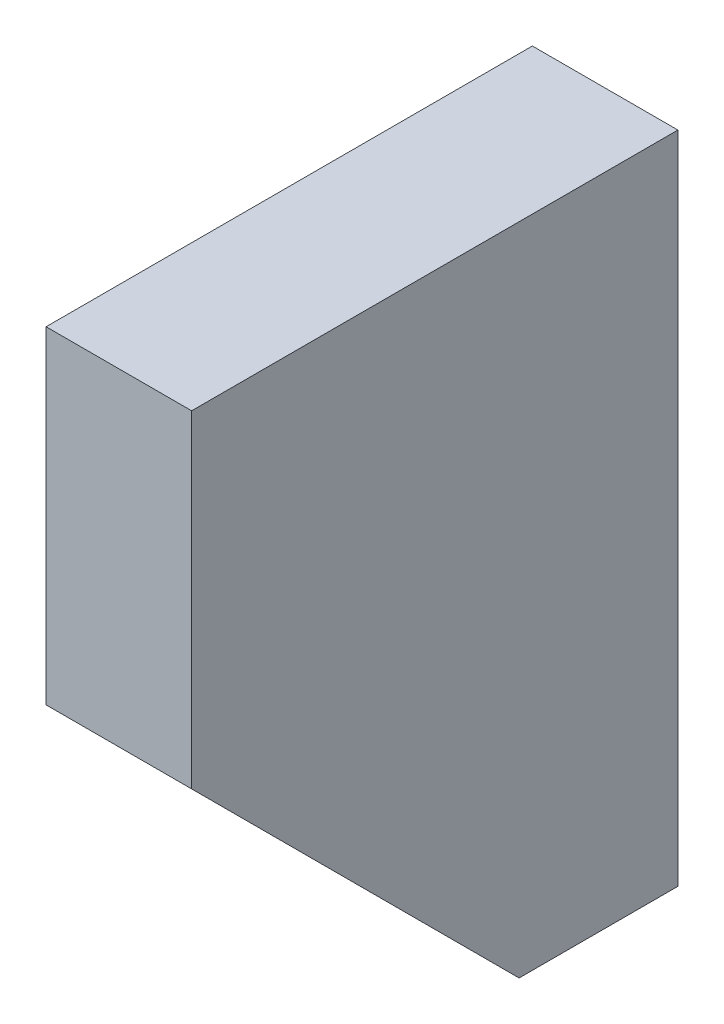
SolidWorks part; units mm, degrees
material "Chêne"
ref_plane "Plan de face" through (0, 0, 0) normal (0, 0, 1) x (1, 0, 0)
ref_plane "Plan de dessus" through (0, 0, 0) normal (0, 1, 0) x (1, 0, 0)
ref_plane "Plan de droite" through (0, 0, 0) normal (1, 0, 0) x (0, 0, -1)
sketch "Esquisse1" plane through (0, 0, 0) normal (0, 0, 1) x (1, 0, 0)
  line L1 (0, 0) -> (22, 0)
  line L2 (0, 0) -> (0, 99)
  line L3 (0, 99) -> (22, 99)
  line L4 (22, 0) -> (22, 99)
  point P4 (59.2366, 162)
  point P7 (-73.5736, 162)
  point P8 (86.7265, 162)
  point P9 (-429.3495, 205.9977)
  dimension "D1" = 22
  dimension "D2" = 99
extrude "Boss.-Extru.1" add sketch "Esquisse1" along normal blind 73.5
sketch "Esquisse2" plane through (0, 0, 0) normal (-1, 0, 0) x (0, 0, 1)
  line L0 (24, 0) -> (73.5, 49.5)
  line L1 (73.5, 0) -> (0, 0) construction
  line L2 (73.5, 0) -> (73.5, 99) construction
  line L3 (73.5, 49.5) -> (73.5, 0)
  line L4 (73.5, 0) -> (24, 0)
extrude "Enlèv. mat.-Extru.1" cut sketch "Esquisse2" against normal blind 35
